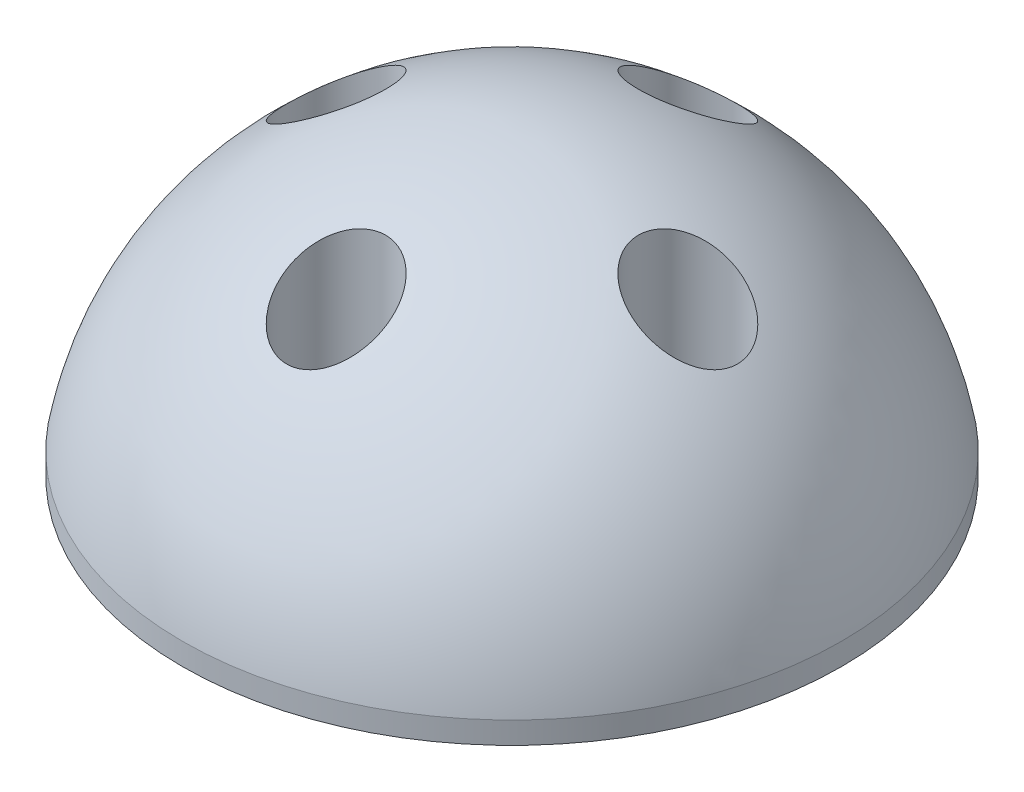
SolidWorks part; units mm, degrees
ref_plane "Front Plane" through (0, 0, 0) normal (0, 0, 1) x (1, 0, 0)
ref_plane "Top Plane" through (0, 0, 0) normal (0, 1, 0) x (1, 0, 0)
ref_plane "Right Plane" through (0, 0, 0) normal (1, 0, 0) x (0, 0, -1)
sketch "Sketch1" plane through (0, 0, 0) normal (0, 1, 0) x (1, 0, 0)
  circle A0 centre (0, 0) radius 15
  dimension "D1" = 30
extrude "Boss-Extrude1" add sketch "Sketch1" along normal blind 1
sketch "Sketch2" plane through (0, 0, 0) normal (0, 0, 1) x (1, 0, 0)
  line L0 (0, 1) -> (-15, 1)
  line L1 (15, 1) -> (-15, 1) construction
  line L2 (0, 1) -> (0, 13.5)
  arc A0 (0, 13.5) -> (-15, 1) centre (0, -1.75) ccw
  dimension "D1" = 12.5
revolve "Revolve1" add sketch "Sketch2" angle 360 about L2
sketch "Sketch3" plane through (0, 0, 0) normal (0, -1, 0) x (1, 0, 0)
  line L0 (0, 15) -> (0, -15) construction
  line L1 (15, 0) -> (-15, 0) construction
  circle A0 centre (0, 0) radius 15 construction
  circle A1 centre (0, 8) radius 1.375
  dimension "D1" = 2.75
  dimension "D2" = 8
extrude "Cut-Extrude1" cut sketch "Sketch3" against normal up to surface (11.9858 mm away)
sketch "Sketch6" plane through (0, 0, 0) normal (1, 0, 0) x (0, 0, -1)
  line L0 (0, 0) -> (0, 13.5) construction
  arc A0 (15, 1) -> (-6.625, 11.9858) centre (0, -1.75) ccw construction
pattern_circular "CirPattern1" count 4 over 360 about axis through (0, 0, 0) along (0, 1, 0) of "Cut-Extrude1"
sketch "Sketch8" plane through (0, 0, 0) normal (0, -1, 0) x (1, 0, 0)
  line L0 (-8, 0) -> (0, 0) construction
  circle A0 centre (-8, 0) radius 2.25
  dimension "D1" = 4.5
extrude "Cut-Extrude2" cut sketch "Sketch8" against normal up to surface (10.5367 mm away) from offset 0.5 offset against normal yes
pattern_circular "CirPattern2" count 4 over 360 about axis through (0, 0, 0) along (0, 1, 0) of "Cut-Extrude2"
